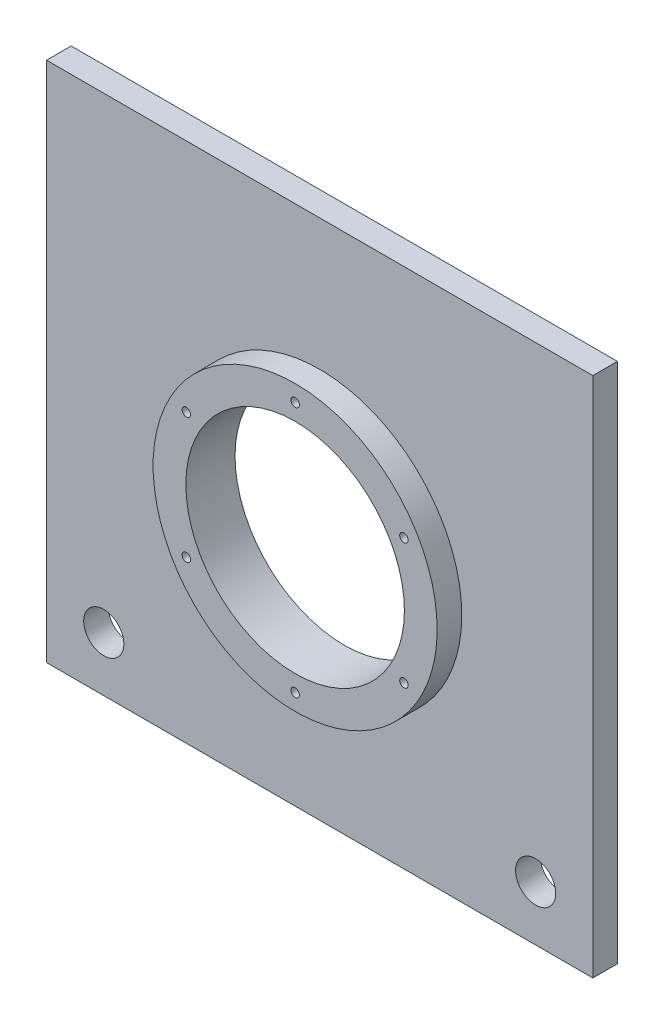
SolidWorks part; units mm, degrees
ref_plane "前视基准面" through (0, 0, 0) normal (0, 0, 1) x (1, 0, 0)
ref_plane "上视基准面" through (0, 0, 0) normal (0, 1, 0) x (1, 0, 0)
ref_plane "右视基准面" through (0, 0, 0) normal (1, 0, 0) x (0, 0, -1)
other "Configuration Table"
sketch "草图1" plane through (0, 0, 0) normal (0, 0, 1) x (1, 0, 0)
  line L0 (0, -1000) -> (0, 49000) construction
  line L1 (-100, 95.5) -> (100, 95.5)
  line L2 (-100, 95.5) -> (-100, -95.5)
  line L3 (-100, -95.5) -> (100, -95.5)
  line L4 (100, 95.5) -> (100, -95.5)
  line L5 (-100, 95.5) -> (100, -95.5) construction
  line L6 (-100, -95.5) -> (100, 95.5) construction
  circle A0 centre (0, -4.5) radius 40
  circle A1 centre (-79.0576, -75.5) radius 7.35
  circle A2 centre (79.0576, -75.5) radius 7.35
  point P0 (0, 0)
  point P18 (48.572, 18.2739)
  point P19 (0, 0)
  point P31 (0, -4.5)
  dimension "D4" = 80
  dimension "D5" = 14.7
  dimension "D1" = 200
  dimension "D2" = 191
  dimension "D3" = 91
  dimension "D6" = 20
extrude "凸台-拉伸1" add sketch "草图1" along normal blind 9
sketch "草图2" plane through (0, 0, 9) normal (0, 0, 1) x (1, 0, 0)
  circle A0 centre (0, -4.5) radius 52
  circle A1 centre (0, -4.5) radius 40 construction
  circle A2 centre (0, -4.5) radius 40
  dimension "D1" = 12
extrude "凸台-拉伸2" add sketch "草图2" along normal blind 9
sketch "草图3" plane through (0, 0, 18) normal (0, 0, 1) x (1, 0, 0)
  line L0 (0, -201000) -> (0, 249000) construction
  line L1 (0, 47.5) -> (0, 35.5) construction
  circle A0 centre (0, 41.5) radius 1.55
  circle A1 centre (0, -4.5) radius 52 construction
  circle A2 centre (0, -4.5) radius 40 construction
  circle A3 centre (39.8372, 18.5) radius 1.55
  circle A4 centre (39.8372, -27.5) radius 1.55
  circle A5 centre (0, -50.5) radius 1.55
  circle A6 centre (-39.8372, -27.5) radius 1.55
  circle A7 centre (-39.8372, 18.5) radius 1.55
  point P10 (0, 0)
  point P11 (0, 41.5)
  point P24 (0, -4.5)
  dimension "D1" = 3.1
  dimension "D2" = 6
extrude "切除-拉伸1" cut sketch "草图3" against normal blind 9
